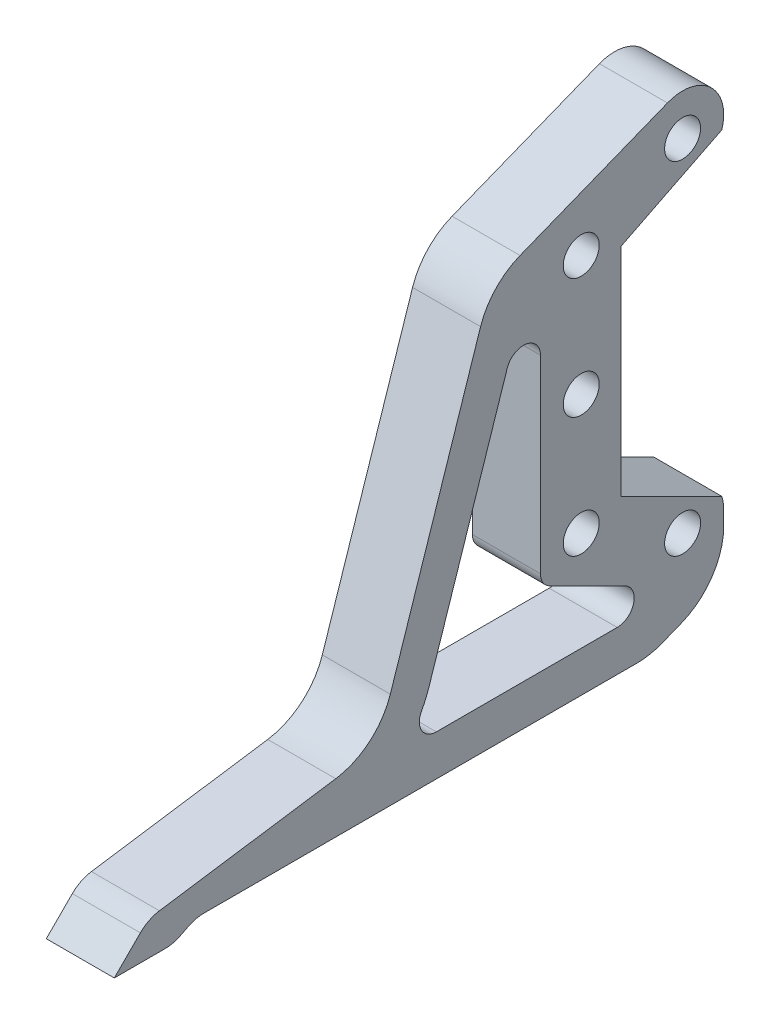
SolidWorks part; units mm, degrees
material "Plain Carbon Steel"
ref_plane "Front Plane" through (0, 0, 0) normal (0, 0, 1) x (1, 0, 0)
ref_plane "Top Plane" through (0, 0, 0) normal (0, 1, 0) x (1, 0, 0)
ref_plane "Right Plane" through (0, 0, 0) normal (1, 0, 0) x (0, 0, -1)
sketch "Sketch1" plane through (0, 0, 0) normal (1, 0, 0) x (0, 0, -1)
  line L0 (-160.655, 50.8) -> (93.345, 50.8)
  line L1 (93.345, 50.8) -> (93.345, -50.8)
  line L2 (93.345, -50.8) -> (-160.655, -50.8)
  line L3 (93.345, 0) -> (55.245, 50.8)
  line L4 (93.345, 0) -> (55.245, -50.8)
  circle A0 centre (0, 0) radius 38.1
  circle A1 centre (0, 0) radius 7.9375
  circle A2 centre (-38.1, 0) radius 7.9375
  circle A3 centre (-88.9, 0) radius 7.9375
  circle A4 centre (-88.9, 0) radius 39.751
  circle A5 centre (-38.1, 0) radius 25.4
  circle A6 centre (-160.655, 0) radius 11.1125
  circle A7 centre (-88.9, 0) radius 23.368
  circle A8 centre (-160.655, 0) radius 33.655
  circle A9 centre (-160.655, 0) radius 76.2
  circle A10 centre (-160.655, 0) radius 50.8
  dimension "D1" = 38.1
  dimension "D3" = 71.755
  dimension "D4" = 15.875
  dimension "D5" = 101.6
  dimension "D9" = 50.8
  dimension "D10" = 67.31
  dimension "D11" = 79.502
  dimension "D12" = 46.736
  dimension "D2" = 50.8
  dimension "D6" = 254
  dimension "D7" = 38.1
  dimension "D8" = 38.1
extrude "Boss-Extrude1" add sketch "Sketch1" along normal blind 12.7 contours A5 A0 A1 | A0 A5 | A10 A7 A9 A3 | A10 A7 A9 A4 | A7 A10 A4 | A7 A10 | A10 A4 A9 A7 | A9 A4 A5 A7 | A10 L2 A9 A4 | A4 A10 A8 | A8 A6 | A10 A4 A9 L0 | A9 A4 A5 A0 L2 L4 L3 L0 | A9 A3 A7 | A4 A5 | A0 A5 A4 A2 | A4 A8
hole_wizard "#8 Clearance Hole1" positions "Sketch3" profile "Sketch4" hole size "#8" standard "ANSI Inch" end condition through all
sketch "Sketch3" plane through (0, 0, 0) normal (-1, 0, 0) x (0, 0, 1)
  point P0 (-17.6911, 17.6911)
  point P3 (17.6911, 17.6911)
  point P6 (17.6911, -17.6911)
  point P9 (-17.6911, -17.6911)
sketch "Sketch4" plane through (0, 17.6911, -17.6911) normal (0, 1, 0) x (0, 0, 1)
  line L0 (0, 0) -> (0, 12.7)
  line L1 (0, 12.7) -> (2.2479, 12.7)
  line L2 (2.2479, 12.7) -> (2.2479, 0)
  line L5 (2.2479, 0) -> (0, 0)
  line L11 (0, -6.35) -> (0, 107.95) construction
  dimension "Thru Hole Dia." = 4.4958
  dimension "Thru Hole Depth" = 12.7
sketch "Sketch5" plane through (0, 0, 0) normal (-1, 0, 0) x (0, 0, 1)
  circle A0 centre (0, 0) radius 18.415
extrude "Cut-Extrude1" cut sketch "Sketch5" against normal through all
sketch "Sketch7" plane through (0, 0, 0) normal (-1, 0, 0) x (0, 0, 1)
  circle A0 centre (-55.245, 0) radius 9.525
  dimension "D1" = 38.1
extrude "Cut-Extrude2" cut sketch "Sketch7" against normal through all
sketch "Sketch8" plane through (12.7, 0, 0) normal (1, 0, 0) x (0, 0, -1)
  line L0 (-160.655, 50.8) -> (-211.455, 25.4)
  line L1 (-211.455, 25.4) -> (-211.455, -25.4)
  line L2 (-211.455, -25.4) -> (-160.655, -50.8)
  line L3 (-160.655, -50.8) -> (-233.2397, -50.8)
  line L4 (-233.2397, -50.8) -> (-233.2397, 50.8)
  line L5 (-233.2397, 50.8) -> (-160.655, 50.8)
  line L6 (-211.455, 0) -> (-160.655, 0) construction
  arc A0 (-160.655, 50.8) -> (-160.655, -50.8) centre (-160.655, 0) ccw construction
  dimension "D1" = 50.8
extrude "Cut-Extrude3" cut sketch "Sketch8" against normal through all
sketch "Sketch9" plane through (12.7, 0, 0) normal (1, 0, 0) x (0, 0, -1)
  line L0 (-160.655, 50.8) -> (-211.455, 25.4)
  line L1 (-211.455, 25.4) -> (-211.455, 0)
  line L2 (-211.455, 0) -> (-211.455, -25.4)
  line L3 (-211.455, -25.4) -> (-160.655, -50.8)
  line L4 (-160.655, -50.8) -> (-160.655, -40.64)
  line L5 (-160.655, -40.64) -> (-202.7493, 0)
  line L6 (-202.7493, 0) -> (-160.655, 40.64)
  line L7 (-160.655, 40.64) -> (-160.655, 50.8)
  line L8 (-160.655, -50.8) -> (-201.295, -30.48) construction
  line L9 (-201.295, 30.48) -> (-160.655, 50.8) construction
  arc A0 (-201.295, 30.48) -> (-201.295, -30.48) centre (-160.655, 0) ccw construction
extrude "Boss-Extrude2" add sketch "Sketch9" against normal blind 12.7
sketch "Sketch10" plane through (0, 0, 0) normal (-1, 0, 0) x (0, 0, 1)
  line L0 (-79.0575, -19.05) -> (-79.0575, 19.05)
  line L1 (-93.345, 0) -> (-55.245, -50.8) construction
  line L3 (-93.345, 0) -> (-55.245, 50.8) construction
  line L4 (-79.0575, 19.05) -> (-93.345, 0)
  line L5 (-93.345, 0) -> (-79.0575, -19.05)
extrude "Cut-Extrude4" cut sketch "Sketch10" against normal through all
sketch "Sketch11" plane through (0, 50.8, 0) normal (0, 1, 0) x (1, 0, 0)
  line L0 (0, -160.655) -> (0, 55.245) construction
  line L1 (0, 36.322) -> (12.7, 36.322)
  line L2 (0, 36.322) -> (0, -141.732)
  line L3 (0, -141.732) -> (12.7, -141.732)
  line L4 (12.7, 36.322) -> (12.7, -141.732)
  line L5 (12.7, -160.655) -> (12.7, 55.245) construction
  line L6 (12.7, -141.605) -> (0, -141.605) construction
  line L7 (0, 36.195) -> (12.7, 36.195) construction
  dimension "D1" = 0.127
  dimension "D2" = 0.127
extrude "Cut-Extrude5" cut sketch "Sketch11" against normal blind 3.175
mirror "Mirror1" about plane through (0, 0, 0) normal (0, 1, 0) of "Cut-Extrude5"
sketch "Sketch12" plane through (12.7, 0, 0) normal (1, 0, 0) x (0, 0, -1)
  line L16 (-162.154, 57.15) -> (-166.9165, 66.675)
  line L17 (-166.9165, 66.675) -> (-185.9665, 66.675)
  line L18 (-185.9665, 66.675) -> (-243.205, 43.9892)
  line L19 (-243.205, 43.9892) -> (-243.205, -43.9892)
  line L20 (-243.205, -43.9892) -> (-185.9665, -66.675)
  line L21 (-185.9665, -66.675) -> (-166.9165, -66.675)
  line L22 (-166.9165, -66.675) -> (-162.154, -57.15)
  line L23 (-243.205, 43.9892) -> (-217.805, 29.3245) construction
  line L24 (-217.805, -29.3245) -> (-243.205, -43.9892) construction
  line L32 (-162.154, -57.15) -> (-135.382, -57.15)
  line L33 (-135.382, -57.15) -> (-135.382, -53.975)
  line L34 (-135.382, -53.975) -> (29.972, -53.975)
  line L35 (29.972, -53.975) -> (29.972, -57.15)
  line L36 (29.972, -57.15) -> (58.42, -57.15)
  line L37 (58.42, -57.15) -> (85.4075, -21.1667)
  line L38 (85.4075, -21.1667) -> (85.4075, 21.1667)
  line L39 (85.4075, 21.1667) -> (58.42, 57.15)
  line L40 (58.42, 57.15) -> (29.972, 57.15)
  line L41 (29.972, 57.15) -> (29.972, 53.975)
  line L42 (29.972, 53.975) -> (-135.382, 53.975)
  line L43 (-135.382, 53.975) -> (-135.382, 57.15)
  line L44 (-135.382, 57.15) -> (-162.154, 57.15)
  line L45 (-162.154, 57.15) -> (-217.805, 29.3245)
  line L46 (-217.805, 29.3245) -> (-217.805, -29.3245)
  line L47 (-217.805, -29.3245) -> (-162.154, -57.15)
  line L48 (-162.154, -57.15) -> (-135.382, -57.15)
  line L49 (-135.382, -57.15) -> (-135.382, -53.975)
  line L50 (-135.382, -53.975) -> (29.972, -53.975)
  line L51 (29.972, -53.975) -> (29.972, -57.15)
  line L52 (29.972, -57.15) -> (58.42, -57.15)
  line L53 (58.42, -57.15) -> (85.4075, -21.1667)
  line L54 (85.4075, -21.1667) -> (85.4075, 21.1667)
  line L55 (85.4075, 21.1667) -> (58.42, 57.15)
  line L56 (58.42, 57.15) -> (29.972, 57.15)
  line L57 (29.972, 57.15) -> (29.972, 53.975)
  line L58 (29.972, 53.975) -> (-135.382, 53.975)
  line L59 (-135.382, 53.975) -> (-135.382, 57.15)
  line L60 (-135.382, 57.15) -> (-162.154, 57.15)
  line L61 (-162.154, 57.15) -> (-217.805, 29.3245)
  line L62 (-217.805, 29.3245) -> (-217.805, -29.3245)
  line L63 (-217.805, -29.3245) -> (-162.154, -57.15)
  circle A0 centre (-160.655, 0) radius 76.2
  dimension "D2" = 9.525
  dimension "D3" = 9.525
  dimension "D4" = 25.4
  dimension "D5" = 120
  dimension "D6" = 120
  dimension "D7" = 19.05
  dimension "D8" = 19.05
  dimension "D1" = 6.35
extrude "Boss-Extrude3" add sketch "Sketch12" against normal blind 19.05 separate body contours A0 L18 L19 L20 | L18 A0 L20 L21 L22 L63 L62 L61 L16 L17
sketch "Sketch13" plane through (12.7, 0, 0) normal (1, 0, 0) x (0, 0, -1)
  line L32 (-161.2546, -53.34) -> (-139.192, -53.34)
  line L33 (-139.192, -53.34) -> (-139.192, -50.165)
  line L34 (-139.192, -50.165) -> (33.782, -50.165)
  line L35 (33.782, -50.165) -> (33.782, -53.34)
  line L36 (33.782, -53.34) -> (56.515, -53.34)
  line L37 (56.515, -53.34) -> (81.5975, -19.8967)
  line L38 (81.5975, -19.8967) -> (81.5975, 19.8967)
  line L39 (81.5975, 19.8967) -> (56.515, 53.34)
  line L40 (56.515, 53.34) -> (33.782, 53.34)
  line L41 (33.782, 53.34) -> (33.782, 50.165)
  line L42 (33.782, 50.165) -> (-139.192, 50.165)
  line L43 (-139.192, 50.165) -> (-139.192, 53.34)
  line L44 (-139.192, 53.34) -> (-161.2546, 53.34)
  line L45 (-161.2546, 53.34) -> (-213.995, 26.9698)
  line L46 (-213.995, 26.9698) -> (-213.995, -26.9698)
  line L47 (-213.995, -26.9698) -> (-161.2546, -53.34)
  line L48 (-161.2546, -53.34) -> (-139.192, -53.34)
  line L49 (-139.192, -53.34) -> (-139.192, -50.165)
  line L50 (-139.192, -50.165) -> (33.782, -50.165)
  line L51 (33.782, -50.165) -> (33.782, -53.34)
  line L52 (33.782, -53.34) -> (56.515, -53.34)
  line L53 (56.515, -53.34) -> (81.5975, -19.8967)
  line L54 (81.5975, -19.8967) -> (81.5975, 19.8967)
  line L55 (81.5975, 19.8967) -> (56.515, 53.34)
  line L56 (56.515, 53.34) -> (33.782, 53.34)
  line L57 (33.782, 53.34) -> (33.782, 50.165)
  line L58 (33.782, 50.165) -> (-139.192, 50.165)
  line L59 (-139.192, 50.165) -> (-139.192, 53.34)
  line L60 (-139.192, 53.34) -> (-161.2546, 53.34)
  line L61 (-161.2546, 53.34) -> (-213.995, 26.9698)
  line L62 (-213.995, 26.9698) -> (-213.995, -26.9698)
  line L63 (-213.995, -26.9698) -> (-161.2546, -53.34)
  dimension "D1" = 2.54
extrude "Cut-Extrude6" cut sketch "Sketch13" against normal through all
hole_wizard "3/8 Clearance Hole1" positions "Sketch15" profile "Sketch14" hole size "3/8" standard "ANSI Inch" end condition through all
sketch "Sketch15" plane through (12.7, 0, 0) normal (1, 0, 0) x (0, 0, -1)
  line L0 (-185.9665, -66.675) -> (-177.394, -49.53) construction
  line L1 (-217.805, -29.3245) -> (-162.154, -57.15) construction
  line L3 (-230.505, 49.0227) -> (-230.505, -49.0227) construction
  line L4 (-185.9665, 66.675) -> (-243.205, 43.9892) construction
  line L5 (-243.205, -43.9892) -> (-185.9665, -66.675) construction
  line L11 (-243.205, 0) -> (-230.505, 0) construction
  line L12 (-243.205, 43.9892) -> (-243.205, -43.9892) construction
  line L13 (-230.505, 0) -> (-217.805, 0) construction
  line L14 (-217.805, 29.3245) -> (-217.805, -29.3245) construction
  line L16 (-181.6803, -58.1025) -> (-230.505, -33.6901) construction
  line L18 (-185.9665, 66.675) -> (-177.394, 49.53) construction
  line L19 (-162.154, 57.15) -> (-217.805, 29.3245) construction
  line L23 (-230.505, 33.6901) -> (-181.6803, 58.1025) construction
  point P0 (-230.505, 0)
  point P2 (-230.505, 33.6901)
  point P4 (-202.1069, 47.8892)
  point P6 (-230.505, -33.6901)
  point P8 (-202.1069, -47.8892)
  dimension "D1" = 31.75
sketch "Sketch14" plane through (12.7, 0, 230.505) normal (0, 1, 0) x (0, 0, -1)
  line L0 (0, 0) -> (0, 19.05)
  line L1 (0, 19.05) -> (5.0419, 19.05)
  line L2 (5.0419, 19.05) -> (5.0419, 0)
  line L5 (5.0419, 0) -> (0, 0)
  line L11 (0, -6.35) -> (0, 107.95) construction
  dimension "Thru Hole Dia." = 10.0838
  dimension "Thru Hole Depth" = 19.05
sketch "Sketch16" plane through (12.7, 0, 0) normal (1, 0, 0) x (0, 0, -1)
  line L16 (-230.505, 0) -> (-132.2223, 0) construction
  line L17 (-132.2223, 0) -> (-132.2223, -76.2) construction
  line L18 (-132.2223, -76.2) -> (-544.0497, -76.2) construction
  line L19 (-219.3925, -30.3056) -> (-162.864, -58.5699)
  line L20 (-219.3925, 30.3056) -> (-219.3925, -30.3056)
  line L21 (-162.864, 58.5699) -> (-219.3925, 30.3056)
  line L22 (-219.3925, -30.3056) -> (-162.864, -58.5699)
  line L23 (-219.3925, 30.3056) -> (-219.3925, -30.3056)
  line L24 (-162.864, 58.5699) -> (-219.3925, 30.3056)
  line L25 (-190.5898, -47.8892) -> (-190.5898, -66.675)
  line L26 (-190.5898, -66.675) -> (-155.601, -66.675)
  line L27 (-155.601, -66.675) -> (-155.601, 66.675)
  line L28 (-155.601, 66.675) -> (-185.9665, 66.675)
  line L29 (-185.9665, 66.675) -> (-206.3505, 58.5961)
  line L30 (-202.1069, 36.372) -> (-202.1069, -36.372)
  circle A0 centre (-202.1069, 47.8892) radius 11.5172
  circle A1 centre (-202.1069, -47.8892) radius 11.5172
  line M9 (-243.205, -43.9892) -> (-185.9665, -66.675)
  line M10 (-185.9665, -66.675) -> (-166.9165, -66.675)
  line M11 (-166.9165, -66.675) -> (-162.154, -57.15)
  line M12 (-162.154, -57.15) -> (-217.805, -29.3245)
  line M13 (-217.805, -29.3245) -> (-217.805, 29.3245)
  line M14 (-217.805, 29.3245) -> (-162.154, 57.15)
  line M15 (-162.154, 57.15) -> (-166.9165, 66.675)
  line M16 (-166.9165, 66.675) -> (-185.9665, 66.675)
  line M17 (-185.9665, 66.675) -> (-243.205, 43.9892)
  dimension "D2" = 76.2
  dimension "D1" = 1.5875
extrude "Cut-Extrude7" cut sketch "Sketch16" against normal through all contours A0 L24 M15 M16 M17 | A0 L24 M14 M15 | L24 A0 M14 | A1 A0 L24 L23 L22 M12 M13 M14 | L22 A1 M12 | A1 L22 M11 M12 | A1 L25 L22 M9 M10 M11
sketch "Sketch17" plane through (12.7, 0, 0) normal (1, 0, 0) x (0, 0, -1)
  line L0 (-230.505, 0) -> (-230.505, -76.2) construction
  line L1 (-230.505, -76.2) -> (-382.905, -76.2) construction
  line L2 (-338.455, -73.025) -> (-211.2347, -73.025)
  line L3 (-211.2347, -73.025) -> (-190.5898, -64.8426)
  line L4 (-190.5898, -64.8426) -> (-243.205, -43.9892)
  line L5 (-243.205, -43.9892) -> (-243.205, 43.9892)
  line L6 (-243.205, 43.9892) -> (-255.905, 38.9557)
  line L7 (-255.905, 38.9557) -> (-287.655, -57.15)
  line L8 (-338.455, -73.025) -> (-344.805, -76.2)
  line L9 (-351.7683, -66.675) -> (-287.655, -57.15)
  line L10 (-344.805, -76.2) -> (-361.2933, -76.2)
  line L11 (-361.2933, -76.2) -> (-351.7683, -66.675)
  line L18 (-206.3505, 58.5961) -> (-243.205, 43.9892) construction
  circle A0 centre (-230.505, -33.6901) radius 5.0419 construction
  circle A1 centre (-230.505, 33.6901) radius 5.0419 construction
  dimension "D1" = 76.2
  dimension "D2" = 15.875
  dimension "D3" = 50.8
  dimension "D4" = 6.35
  dimension "D5" = 6.35
  dimension "D6" = 57.15
  dimension "D7" = 25.4
  dimension "D8" = 6.35
  dimension "D9" = 9.525
extrude "Boss-Extrude4" add sketch "Sketch17" against normal blind 19.05
fillet "Fillet1" radius 19.05 4 edges at (3.175, -64.8426, 190.5898) (3.175, -73.025, 211.2347) (3.175, -57.15, 287.655) (3.175, 38.9557, 255.905)
fillet "Fillet2" radius 9.525 3 edges at (3.175, -76.2, 344.805) (3.175, -73.025, 338.455) (3.175, -66.675, 351.7683)
sketch "Sketch18" plane through (12.7, 0, 0) normal (1, 0, 0) x (0, 0, -1)
  line L60 (-280.5207, -61.595) -> (-214.8722, -61.595)
  line L61 (-212.0645, -61.0589) -> (-206.8321, -58.9851)
  line L62 (-202.0198, -51.9012) -> (-202.0198, -51.7711)
  line L63 (-202.0198, -51.7711) -> (-230.8225, -37.3698)
  line L64 (-230.8225, -37.3698) -> (-230.8225, 36.6019)
  line L65 (-230.505, 33.6901) -> (-230.505, -33.6901) construction
  line L66 (-230.8225, 36.6019) -> (-243.4169, 31.6102)
  line L67 (-247.8447, 26.9166) -> (-273.1207, -49.5926)
  line L68 (-280.5207, -61.595) -> (-214.8722, -61.595)
  line L69 (-212.0645, -61.0589) -> (-206.8321, -58.9851)
  line L70 (-202.0198, -51.9012) -> (-202.0198, -51.7711)
  line L71 (-202.0198, -51.7711) -> (-230.8225, -37.3698)
  line L72 (-230.8225, -37.3698) -> (-230.8225, 36.6019)
  line L73 (-230.505, -33.6901) -> (-202.1069, -47.8892) construction
  line L74 (-230.8225, 36.6019) -> (-243.4169, 31.6102)
  line L75 (-247.8447, 26.9166) -> (-273.1207, -49.5926)
  line L76 (-241.935, 33.6901) -> (-241.935, -40.7543)
  line L77 (-241.935, -40.7543) -> (-207.2186, -58.1125)
  line L78 (-207.2186, -58.1125) -> (-206.1221, -58.6607)
  line L88 (-202.0198, -51.7711) -> (-202.0173, -51.7696)
  line L89 (-202.0198, -51.7711) -> (-202.0173, -51.7696)
  arc A45 (-214.8722, -61.595) -> (-212.0645, -61.0589) centre (-214.8722, -53.975) ccw
  arc A46 (-206.8321, -58.9851) -> (-202.0198, -51.9012) centre (-209.6398, -51.9012) ccw
  circle A47 centre (-202.1069, -47.8892) radius 5.0419 construction
  arc A48 (-243.4169, 31.6102) -> (-247.8447, 26.9166) centre (-240.6093, 24.5263) ccw
  arc A49 (-280.5207, -61.595) -> (-273.1207, -49.5926) centre (-302.0622, -40.0313) ccw
  arc A50 (-214.8722, -61.595) -> (-212.0645, -61.0589) centre (-214.8722, -53.975) ccw
  arc A51 (-206.8321, -58.9851) -> (-202.0198, -51.9012) centre (-209.6398, -51.9012) ccw
  circle A52 centre (-230.505, -33.6901) radius 5.0419 construction
  arc A53 (-243.4169, 31.6102) -> (-247.8447, 26.9166) centre (-240.6093, 24.5263) ccw
  arc A54 (-280.5207, -61.595) -> (-273.1207, -49.5926) centre (-302.0622, -40.0313) ccw
  dimension "D2" = 11.43
  dimension "D1" = 11.43
extrude "Cut-Extrude8" cut sketch "Sketch18" against normal through all contours A54 L68 A50 L69 A51 L78 L77 L76 L74 A53 L75
sketch "Sketch19" plane through (12.7, 0, 0) normal (1, 0, 0) x (0, 0, -1)
  line L0 (-241.935, -40.7543) -> (-206.1221, -58.6607) construction
  line L1 (-247.8447, 26.9166) -> (-273.1207, -49.5926) construction
  line L2 (-241.935, 32.1976) -> (-241.935, -40.7543) construction
  line L3 (-280.5207, -61.595) -> (-214.8722, -61.595) construction
  line L4 (-247.8447, 26.9166) -> (-273.1207, -49.5926)
  line L5 (-280.5207, -61.595) -> (-214.8722, -61.595)
  line L6 (-241.935, -40.7543) -> (-206.1221, -58.6607)
  line L7 (-241.935, 32.1976) -> (-241.935, -40.7543)
  line L16 (-361.2933, -76.2) -> (-347.0535, -76.2)
  line L17 (-342.7938, -75.1944) -> (-340.4662, -74.0306)
  line L18 (-336.2065, -73.025) -> (-214.8722, -73.025)
  line L19 (-207.8531, -71.6848) -> (-202.6207, -69.611)
  line L20 (-190.5898, -51.9012) -> (-190.5898, -47.8892)
  line L21 (-191.1174, -44.4432) -> (-219.3925, -30.3056)
  line L22 (-219.3925, -30.3056) -> (-219.3925, 30.3056)
  line L23 (-219.3925, 30.3056) -> (-191.1174, 44.4432)
  line L24 (-206.3505, 58.5961) -> (-247.6284, 42.2361)
  line L25 (-258.6978, 30.5021) -> (-283.9738, -46.0071)
  line L26 (-299.2628, -58.8745) -> (-348.657, -66.2128)
  line L27 (-353.9925, -68.8992) -> (-361.2933, -76.2)
  line L28 (-361.2933, -76.2) -> (-347.0535, -76.2)
  line L29 (-342.7938, -75.1944) -> (-340.4662, -74.0306)
  line L30 (-336.2065, -73.025) -> (-214.8722, -73.025)
  line L31 (-207.8531, -71.6848) -> (-202.6207, -69.611)
  line L32 (-190.5898, -51.9012) -> (-190.5898, -47.8892)
  line L33 (-191.1174, -44.4432) -> (-219.3925, -30.3056)
  line L34 (-219.3925, -30.3056) -> (-219.3925, 30.3056)
  line L35 (-219.3925, 30.3056) -> (-191.1174, 44.4432)
  line L36 (-206.3505, 58.5961) -> (-247.6284, 42.2361)
  line L37 (-258.6978, 30.5021) -> (-283.9738, -46.0071)
  line L38 (-299.2628, -58.8745) -> (-348.657, -66.2128)
  line L39 (-353.9925, -68.8992) -> (-361.2933, -76.2)
  circle A0 centre (-246.6975, 15.207) radius 4.7625
  circle A1 centre (-271.0823, -56.8325) radius 4.7625
  circle A2 centre (-220.4278, -56.8325) radius 4.7625
  arc A3 (-280.5207, -61.595) -> (-273.1207, -49.5926) centre (-302.0622, -40.0313) ccw construction
  arc A4 (-280.5207, -61.595) -> (-273.1207, -49.5926) centre (-302.0622, -40.0313) ccw
  arc A13 (-347.0535, -76.2) -> (-342.7938, -75.1944) centre (-347.0535, -66.675) ccw
  arc A14 (-336.2065, -73.025) -> (-340.4662, -74.0306) centre (-336.2065, -82.55) ccw
  arc A15 (-214.8722, -73.025) -> (-207.8531, -71.6848) centre (-214.8722, -53.975) ccw
  arc A16 (-202.6207, -69.611) -> (-190.5898, -51.9012) centre (-209.6398, -51.9012) ccw
  arc A17 (-190.5898, -47.8892) -> (-191.1174, -44.4432) centre (-202.1069, -47.8892) ccw
  arc A18 (-191.1174, 44.4432) -> (-206.3505, 58.5961) centre (-202.1069, 47.8892) ccw
  arc A19 (-247.6284, 42.2361) -> (-258.6978, 30.5021) centre (-240.6093, 24.5263) ccw
  arc A20 (-299.2628, -58.8745) -> (-283.9738, -46.0071) centre (-302.0622, -40.0313) ccw
  arc A21 (-348.657, -66.2128) -> (-353.9925, -68.8992) centre (-347.2573, -75.6344) ccw
  arc A22 (-347.0535, -76.2) -> (-342.7938, -75.1944) centre (-347.0535, -66.675) ccw
  arc A23 (-336.2065, -73.025) -> (-340.4662, -74.0306) centre (-336.2065, -82.55) ccw
  arc A24 (-214.8722, -73.025) -> (-207.8531, -71.6848) centre (-214.8722, -53.975) ccw
  arc A25 (-202.6207, -69.611) -> (-190.5898, -51.9012) centre (-209.6398, -51.9012) ccw
  arc A26 (-190.5898, -47.8892) -> (-191.1174, -44.4432) centre (-202.1069, -47.8892) ccw
  arc A27 (-191.1174, 44.4432) -> (-206.3505, 58.5961) centre (-202.1069, 47.8892) ccw
  arc A28 (-247.6284, 42.2361) -> (-258.6978, 30.5021) centre (-240.6093, 24.5263) ccw
  arc A29 (-299.2628, -58.8745) -> (-283.9738, -46.0071) centre (-302.0622, -40.0313) ccw
  arc A30 (-348.657, -66.2128) -> (-353.9925, -68.8992) centre (-347.2573, -75.6344) ccw
  line M48 (-214.8722, -61.595) -> (-280.5207, -61.595)
  arc M49 (-280.5207, -61.595) -> (-273.1207, -49.5926) centre (-302.0622, -40.0313) ccw
  arc M51 (-247.8447, 26.9166) -> (-243.4169, 31.6102) centre (-240.6093, 24.5263) cw
  line M52 (-243.4169, 31.6102) -> (-241.935, 32.1976)
  line M53 (-241.935, 32.1976) -> (-241.935, -40.7543)
  arc M55 (-206.1221, -58.6607) -> (-206.8321, -58.9851) centre (-209.6398, -51.9012) cw
  line M56 (-206.8321, -58.9851) -> (-212.0645, -61.0589)
  arc M57 (-212.0645, -61.0589) -> (-214.8722, -61.595) centre (-214.8722, -53.975) cw
  dimension "D1" = 9.525
  dimension "D2" = 0
extrude "Boss-Extrude5" add sketch "Sketch19" against normal up to surface (19.05 mm away) contours A0 L4 M53 M52 M51 | A1 L5 M49 | A2 L6 M48 M57 M56 M55 up to face at (-6.35, 0, 225.4631)
fillet "Fillet3" radius 4.7625 1 edges at (3.175, -40.7543, 241.935)
